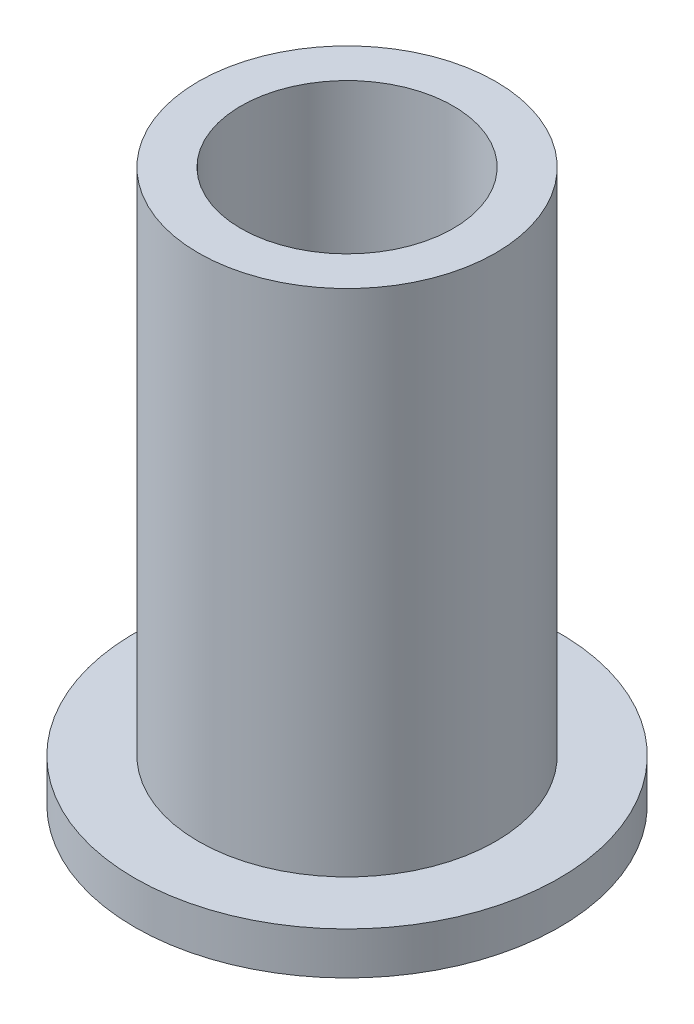
SolidWorks part; units mm, degrees
ref_plane "Front Plane" through (0, 0, 0) normal (0, 0, 1) x (1, 0, 0)
ref_plane "Top Plane" through (0, 0, 0) normal (0, 1, 0) x (1, 0, 0)
ref_plane "Right Plane" through (0, 0, 0) normal (1, 0, 0) x (0, 0, -1)
sketch "Sketch1" plane through (0, 0, 0) normal (0, 1, 0) x (1, 0, 0)
  circle A0 centre (0, 0) radius 5
  dimension "D1" = 10
extrude "Boss-Extrude1" add sketch "Sketch1" along normal blind 1
sketch "Sketch2" plane through (0, 1, 0) normal (0, 1, 0) x (1, 0, 0)
  circle A0 centre (0, 0) radius 3.5
  dimension "D1" = 7
extrude "Boss-Extrude2" add sketch "Sketch2" along normal blind 12
sketch "Sketch3" plane through (0, 13, 0) normal (0, 1, 0) x (1, 0, 0)
  circle A0 centre (0, 0) radius 2.5
  dimension "D1" = 5
extrude "Cut-Extrude1" cut sketch "Sketch3" against normal up to surface (13 mm away) up to face at (0, 0, 5)
